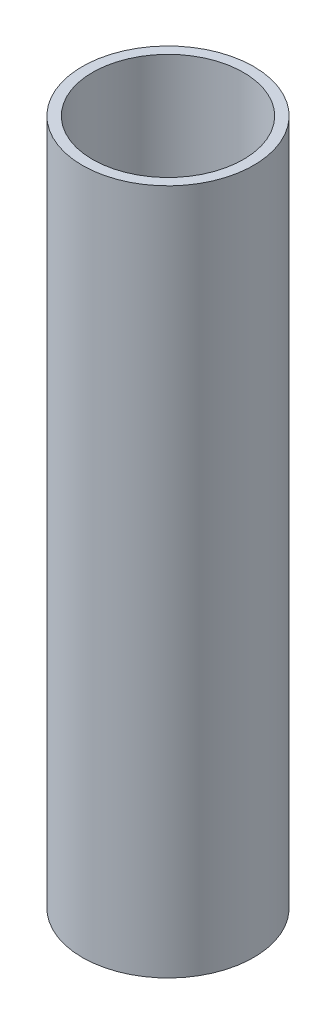
SolidWorks part; units mm, degrees
ref_plane "Front" through (0, 0, 0) normal (0, 0, 1) x (1, 0, 0)
ref_plane "Top" through (0, 0, 0) normal (0, 1, 0) x (1, 0, 0)
ref_plane "Right" through (0, 0, 0) normal (1, 0, 0) x (0, 0, -1)
sketch "Sketch1" plane through (0, 0, 0) normal (0, 1, 0) x (1, 0, 0)
  circle A0 centre (0, 0) radius 12.6873
  circle A1 centre (0, 0) radius 11.176
  dimension "D1" = 25.3746
  dimension "D2" = 22.352
extrude "Boss-Extrude1" add sketch "Sketch1" along normal blind 101.6
